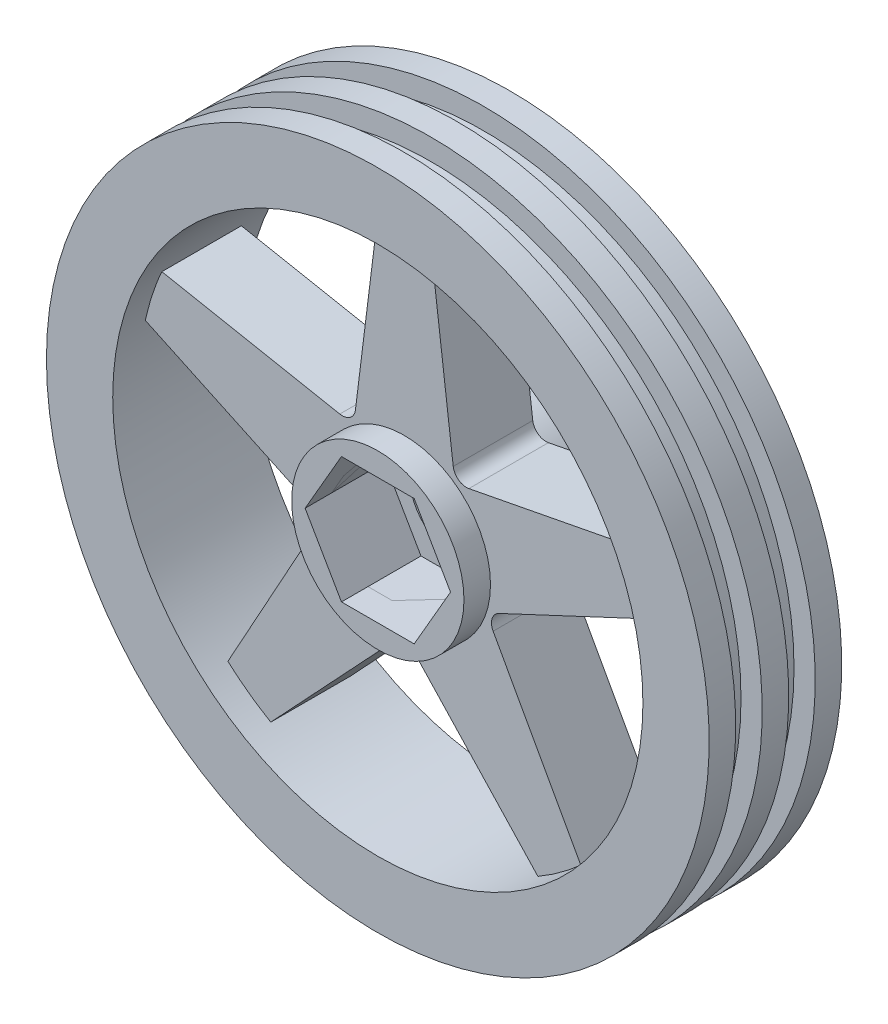
SolidWorks part; units mm, degrees
ref_plane "Front" through (0, 0, 0) normal (0, 0, 1) x (1, 0, 0)
ref_plane "Top" through (0, 0, 0) normal (0, 1, 0) x (1, 0, 0)
ref_plane "Right" through (0, 0, 0) normal (1, 0, 0) x (0, 0, -1)
sketch "Sketch1" plane through (0, 0, 0) normal (0, 1, 0) x (1, 0, 0)
  line L0 (-31.75, 0) -> (0, 0) construction
  line L1 (-25.4, 6.35) -> (-31.75, 6.35)
  line L3 (-31.75, -6.35) -> (-25.4, -6.35)
  line L5 (-31.75, -6.35) -> (-31.75, -3.81)
  line L6 (-31.75, -3.81) -> (-29.718, -3.81)
  line L7 (-29.718, -3.81) -> (-29.718, -1.27)
  line L8 (-29.718, -1.27) -> (-31.75, -1.27)
  line L9 (-31.75, -1.27) -> (-31.75, 1.27)
  line L10 (-31.75, 1.27) -> (-29.718, 1.27)
  line L11 (-29.718, 1.27) -> (-29.718, 3.81)
  line L12 (-29.718, 3.81) -> (-31.75, 3.81)
  line L13 (-31.75, 3.81) -> (-31.75, 6.35)
  line L14 (-25.4, 6.35) -> (-25.4, -6.35)
  line L15 (0, 7.1501) -> (0, -7.1501) construction
  dimension "D1" = 12.7
  dimension "D2" = 31.75
  dimension "D3" = 2.54
  dimension "D4" = 2.032
  dimension "D5" = 6.35
revolve "Revolve1" add sketch "Sketch1" angle 360 about L15
sketch "Sketch2" plane through (0, 0, 0) normal (0, 0, 1) x (1, 0, 0)
  circle A0 centre (0, 0) radius 8.255
  dimension "D2" = 16.51
extrude "Boss-Extrude1" add sketch "Sketch2" along normal mid plane 12.7 separate body
sketch "Sketch3" plane through (0, 0, 0) normal (0, 0, 1) x (1, 0, 0)
  line L0 (-4.6846, 8.0258) -> (-2.54, 25.2727)
  line L1 (0, 25.4) -> (0, -25.4) construction
  line L2 (2.54, 25.2727) -> (4.6846, 8.0258)
  line L3 (6.1853, 6.9354) -> (23.2508, 10.2254)
  line L4 (24.8207, 5.394) -> (9.0806, -1.9752)
  line L5 (8.5074, -3.7394) -> (16.9098, -18.9531)
  line L6 (12.8, -21.939) -> (0.9275, -9.2465)
  line L7 (-0.9275, -9.2465) -> (-12.8, -21.939)
  line L8 (-16.9098, -18.9531) -> (-8.5074, -3.7394)
  line L9 (-9.0806, -1.9752) -> (-24.8207, 5.394)
  line L10 (-23.2508, 10.2254) -> (-6.1853, 6.9354)
  circle A0 centre (0, 0) radius 8.255 construction
  circle A1 centre (0, 0) radius 8.255
  circle A2 centre (0, 0) radius 25.4 construction
  arc A3 (-23.2508, 10.2254) -> (-24.8207, 5.394) centre (0, 0) ccw
  arc A4 (2.54, 25.2727) -> (-2.54, 25.2727) centre (0, 0) ccw
  arc A5 (24.8207, 5.394) -> (23.2508, 10.2254) centre (0, 0) ccw
  arc A6 (12.8, -21.939) -> (16.9098, -18.9531) centre (0, 0) ccw
  arc A7 (-16.9098, -18.9531) -> (-12.8, -21.939) centre (0, 0) ccw
  arc A8 (-8.5074, -3.7394) -> (-9.0806, -1.9752) centre (-9.6191, -3.1254) ccw
  arc A9 (0.9275, -9.2465) -> (-0.9275, -9.2465) centre (0, -10.1141) ccw
  arc A10 (9.0806, -1.9752) -> (8.5074, -3.7394) centre (9.6191, -3.1254) ccw
  arc A11 (4.6846, 8.0258) -> (6.1853, 6.9354) centre (5.9449, 8.1825) ccw
  arc A12 (-4.6846, 8.0258) -> (-6.1853, 6.9354) centre (-5.9449, 8.1825) cw
  point P31 (0, 0)
  point P33 (4.8522, 6.6784)
  point P36 (-4.8522, 6.6784)
  dimension "D1" = 1.27
  dimension "D2" = 5.08
  dimension "D3" = 5
extrude "Boss-Extrude3" add sketch "Sketch3" along normal mid plane 7.62 separate body contours L6 A6 L5 L4 A1 L7 | L4 A5 L3 L2 A1 L5 | L10 A3 L9 L8 A1 L0 | L8 A7 L7 L6 A1 L9 | A4 L1 A1 L3 L2 | L1 A4 L0 L10 A1
sketch "Sketch4" plane through (0, 0, 6.35) normal (0, 0, 1) x (1, 0, 0)
  line L1 (3.4829, 6.0325) -> (-3.4829, 6.0325)
  line L2 (-3.4829, 6.0325) -> (-6.9657, 0)
  line L3 (-6.9657, 0) -> (-3.4829, -6.0325)
  line L4 (-3.4829, -6.0325) -> (3.4829, -6.0325)
  line L5 (3.4829, -6.0325) -> (6.9657, 0)
  line L6 (6.9657, 0) -> (3.4829, 6.0325)
  circle A0 centre (0, 0) radius 6.0325 construction
  dimension "D1" = 12.065
extrude "Cut-Extrude1" cut sketch "Sketch4" against normal blind 7.62
sketch "Sketch5" plane through (0, 0, -1.27) normal (0, 0, 1) x (1, 0, 0)
  circle A0 centre (0, 0) radius 4.572
  dimension "D1" = 9.144
extrude "Cut-Extrude2" cut sketch "Sketch5" against normal through all
